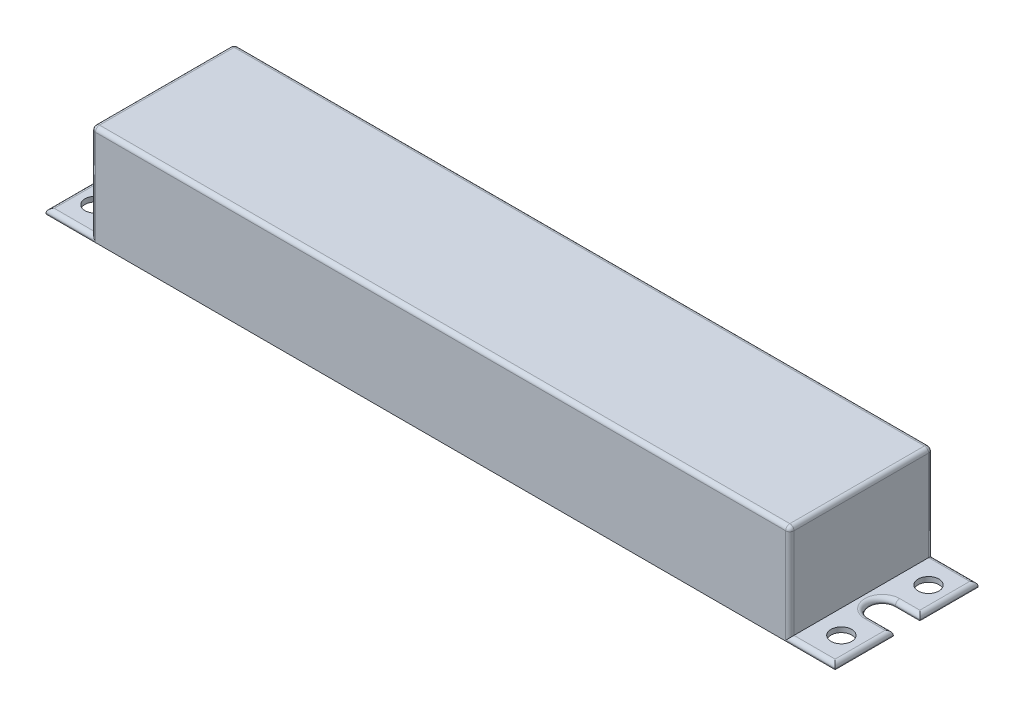
SolidWorks part; units mm, degrees
ref_plane "Front Plane" through (0, 0, 0) normal (0, 0, 1) x (1, 0, 0)
ref_plane "Top Plane" through (0, 0, 0) normal (0, 1, 0) x (1, 0, 0)
ref_plane "Right Plane" through (0, 0, 0) normal (1, 0, 0) x (0, 0, -1)
sketch "Sketch1" plane through (0, 0, 0) normal (0, 1, 0) x (1, 0, 0)
  line L1 (-120.65, -21.844) -> (120.65, -21.844)
  line L2 (-120.65, -21.844) -> (-120.65, 21.844)
  line L3 (-120.65, 21.844) -> (120.65, 21.844)
  line L4 (120.65, -21.844) -> (120.65, 21.844)
  line L5 (-120.65, -21.844) -> (120.65, 21.844) construction
  line L6 (-120.65, 21.844) -> (120.65, -21.844) construction
  point P0 (0, 0)
  dimension "D1" = 43.688
  dimension "D2" = 241.3
extrude "Boss-Extrude1" add sketch "Sketch1" along normal blind 1.524
hole_wizard "1/4 (0.25) Diameter Hole1" positions "Sketch2" profile "Sketch3" hole size "1/4" standard "ANSI Inch" end condition through all
sketch "Sketch2" plane through (0, 1.524, 0) normal (0, 1, 0) x (1, 0, 0)
  line L0 (-114.046, 21.844) -> (-114.046, -21.844) construction
  line L1 (120.65, 21.844) -> (-120.65, 21.844) construction
  line L2 (-120.65, -21.844) -> (120.65, -21.844) construction
  line L4 (114.046, 21.844) -> (114.046, -21.844) construction
  line L6 (-120.65, 21.844) -> (-120.65, -21.844) construction
  line L7 (120.65, -21.844) -> (120.65, 21.844) construction
  line L9 (-120.65, 0) -> (120.65, 0) construction
  point P22 (-114.046, 13.335)
  point P24 (-114.046, -13.335)
  point P25 (114.046, 13.335)
  point P27 (114.046, -13.335)
  dimension "D1" = 6.604
  dimension "D2" = 6.604
  dimension "D3" = 26.67
  dimension "D4" = 13.335
sketch "Sketch3" plane through (114.046, 1.524, 13.335) normal (1, 0, 0) x (0, 0, 1)
  line L0 (0, 0) -> (0, 1.524)
  line L1 (0, 1.524) -> (3.175, 1.524)
  line L2 (3.175, 1.524) -> (3.175, 0)
  line L5 (3.175, 0) -> (0, 0)
  line L11 (0, -6.35) -> (0, 107.95) construction
  dimension "Thru Hole Dia." = 6.35
  dimension "Thru Hole Depth" = 1.524
sketch "Sketch4" plane through (0, 1.524, 0) normal (0, 1, 0) x (1, 0, 0)
  line L0 (-128.0795, 0) -> (-113.2205, 0) construction
  line L1 (-120.65, 21.844) -> (-120.65, -21.844) construction
  line L2 (-120.65, 4.064) -> (-113.2205, 4.064)
  line L3 (-120.65, -4.064) -> (-113.2205, -4.064)
  line L4 (-120.65, 4.064) -> (-120.65, -4.064)
  line L5 (113.2205, 0) -> (128.0795, 0) construction
  line L6 (113.2205, 4.064) -> (120.65, 4.064)
  line L7 (113.2205, -4.064) -> (120.65, -4.064)
  line L8 (120.65, 4.064) -> (120.65, -4.064)
  arc A1 (-113.2205, -4.064) -> (-113.2205, 4.064) centre (-113.2205, 0) ccw
  arc A2 (113.2205, 4.064) -> (113.2205, -4.064) centre (113.2205, 0) ccw
  point P5 (-120.65, 0)
  point P15 (120.65, 0)
  dimension "D2" = 8.128
extrude "Cut-Extrude1" cut sketch "Sketch4" against normal through all
sketch "Sketch5" plane through (0, 1.524, 0) normal (0, 1, 0) x (1, 0, 0)
  line L0 (-120.65, 21.844) -> (120.65, -21.844) construction
  line L2 (-106.807, -21.844) -> (106.807, -21.844)
  line L3 (-106.807, -21.844) -> (-106.807, 21.844)
  line L4 (-106.807, 21.844) -> (106.807, 21.844)
  line L5 (106.807, -21.844) -> (106.807, 21.844)
  line L6 (-106.807, -21.844) -> (106.807, 21.844) construction
  line L7 (-106.807, 21.844) -> (106.807, -21.844) construction
  point P4 (0, 0)
  dimension "D1" = 213.614
extrude "Boss-Extrude2" add sketch "Sketch5" along normal blind 28.956
fillet "Fillet2" radius 1.27 22 edges at (116.9352, 1.524, -4.064) (116.9352, 1.524, 4.064) (-116.9353, 1.524, 4.064) (-116.9353, 1.524, -4.064) (113.7285, 1.524, 21.844) (120.65, 1.524, 12.954) (109.1565, 1.524, 0) (120.65, 1.524, -12.954) (113.7285, 1.524, -21.844) (-106.807, 16.002, 21.844) (-109.1565, 1.524, 0) (-113.7285, 1.524, 21.844) (-113.7285, 1.524, -21.844) (-120.65, 1.524, -12.954) (-120.65, 1.524, 12.954) (-106.807, 16.002, -21.844) (106.807, 16.002, -21.844) (106.807, 16.002, 21.844) (106.807, 30.48, 0) (0, 30.48, -21.844) (-106.807, 30.48, 0) (0, 30.48, 21.844)
